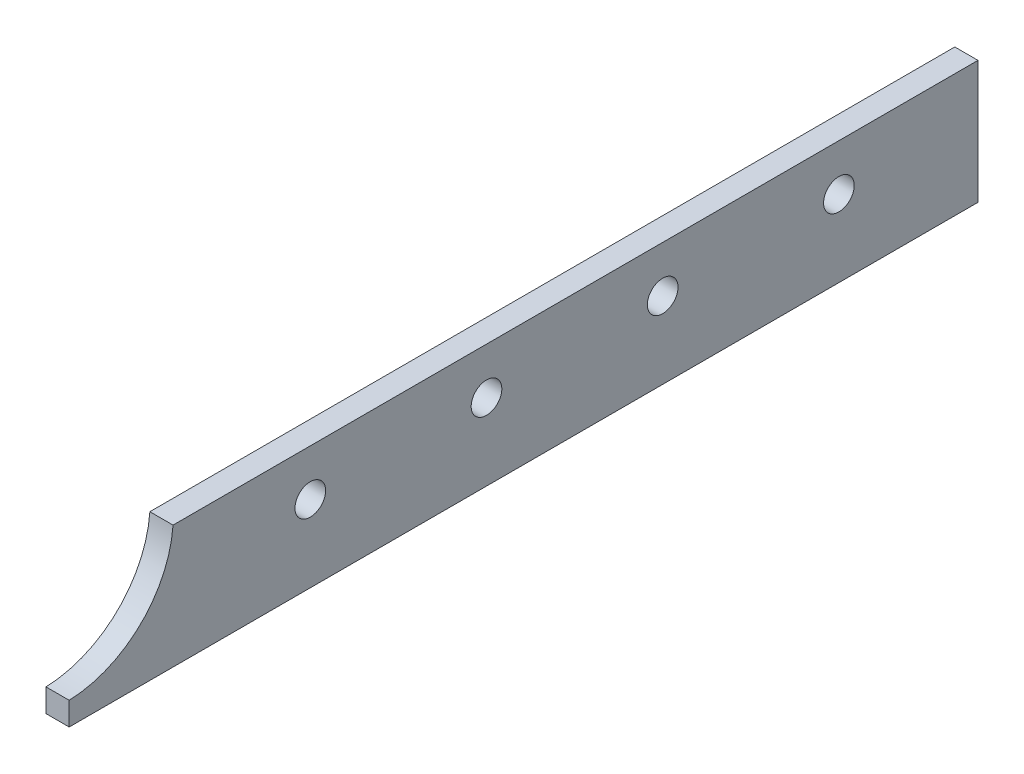
SolidWorks part; units mm, degrees
material "Silicon Rubber"
ref_plane "Front Plane" through (0, 0, 0) normal (0, 0, 1) x (1, 0, 0)
ref_plane "Top Plane" through (0, 0, 0) normal (0, 1, 0) x (1, 0, 0)
ref_plane "Right Plane" through (0, 0, 0) normal (1, 0, 0) x (0, 0, -1)
sketch "Sketch1" plane through (0, 0, 0) normal (1, 0, 0) x (0, 0, -1)
  line L10 (-49.3055, 3.3458) -> (62.23, -8.4201) construction
  line L13 (-62.23, -8.4201) -> (62.23, -8.4201)
  line L14 (-62.23, -8.4201) -> (-62.23, -5.2451)
  line L15 (-48.006, 8.4201) -> (62.23, 8.4201)
  line L16 (62.23, -8.4201) -> (62.23, 8.4201)
  line L17 (-62.23, -8.4201) -> (62.23, 8.4201) construction
  arc A1 (-62.23, -5.2451) -> (-48.006, 8.4201) centre (-62.6999, 9.4794) ccw
  point P0 (0, 0)
  dimension "D2" = 14.732
  dimension "D3" = 14.224
  dimension "D1" = 16.8402
  dimension "D4" = 110.236
  dimension "D5" = 3.175
  dimension "D6" = 8.4201
extrude "Boss-Extrude1" add sketch "Sketch1" along normal blind 3.175
sketch "Sketch3" plane through (0, 0, 0) normal (-1, 0, 0) x (0, 0, 1)
  line L0 (-62.23, 8.4201) -> (-62.23, -4.2799) construction
  line L1 (-62.23, -8.4201) -> (-62.23, 8.4201) construction
  line L2 (-62.23, 2.0701) -> (53.896, 2.0701) construction
  circle A1 centre (-43.18, 2.0701) radius 2.1
  circle A2 centre (-19.05, 2.0701) radius 2.1
  circle A3 centre (5.08, 2.0701) radius 2.1
  circle A4 centre (29.21, 2.0701) radius 2.1
  dimension "D2" = 4.2
  dimension "D3" = 19.05
  dimension "D1" = 12.7
  dimension "D4" = 24.13
  dimension "D5" = 24.13
  dimension "D6" = 24.13
  dimension "D7" = 116.126
extrude "Cut-Extrude1" cut sketch "Sketch3" against normal through all
